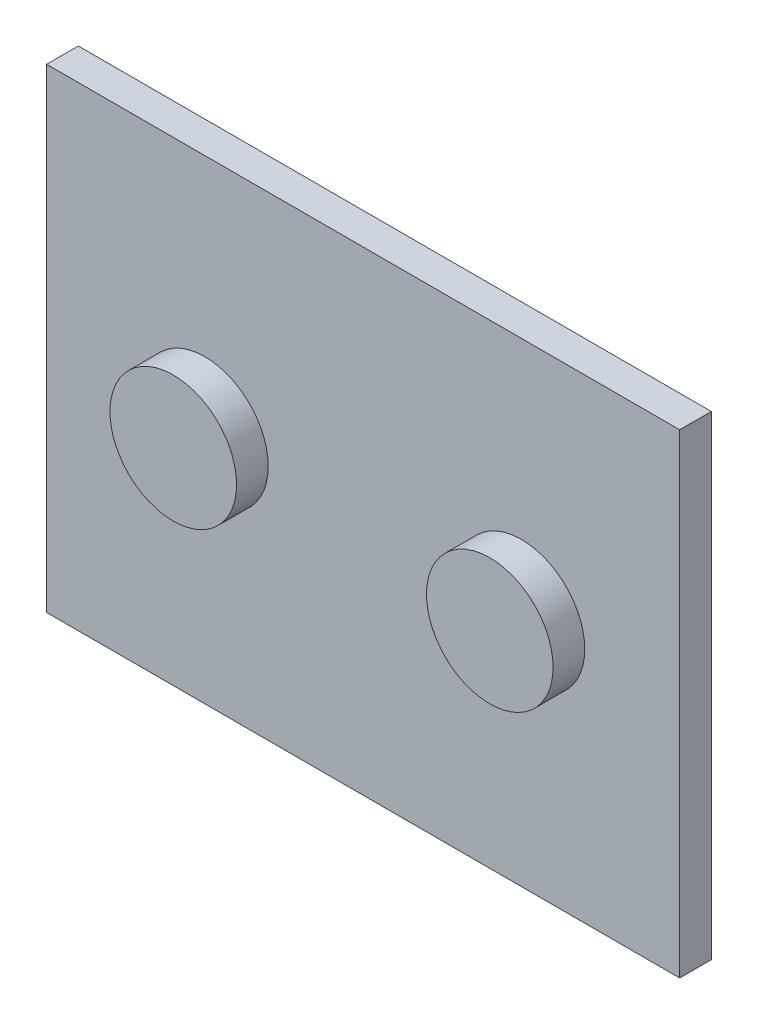
SolidWorks part; units mm, degrees
ref_plane "Front Plane" through (0, 0, 0) normal (0, 0, 1) x (1, 0, 0)
ref_plane "Top Plane" through (0, 0, 0) normal (0, 1, 0) x (1, 0, 0)
ref_plane "Right Plane" through (0, 0, 0) normal (1, 0, 0) x (0, 0, -1)
sketch "Sketch1" plane through (0, 0, 0) normal (0, 0, 1) x (1, 0, 0)
  line L1 (-101.369, 69.9691) -> (98.631, 69.9691)
  line L2 (-101.369, 69.9691) -> (-101.369, -80.0309)
  line L3 (-101.369, -80.0309) -> (98.631, -80.0309)
  line L4 (98.631, 69.9691) -> (98.631, -80.0309)
  dimension "D1" = 200
  dimension "D2" = 150
extrude "Boss-Extrude2" add sketch "Sketch1" along normal blind 10
sketch "Sketch2" plane through (0, 0, 10) normal (0, 0, 1) x (1, 0, 0)
  line L0 (-101.369, 69.9691) -> (98.631, -80.0309)
  line L1 (98.631, -80.0309) -> (98.631, 69.9691)
  line L2 (98.631, 69.9691) -> (-101.369, -80.0309)
  line L3 (-51.369, -5.0309) -> (48.631, -5.0309)
  circle A0 centre (-1.369, -5.0309) radius 50
  circle A1 centre (-51.369, -5.0309) radius 20
  circle A2 centre (48.631, -5.0309) radius 20
  dimension "D1" = 100
extrude "Boss-Extrude3" add sketch "Sketch2" along normal blind 10 contours A0 A2 | A0 A2 L3 | L3 A2 A0 | A1
sketch "Sketch3" plane through (0, 0, 20) normal (0, 0, 1) x (1, 0, 0)
  line L0 (-71.369, -5.0309) -> (-31.369, -5.0309)
  circle A0 centre (-51.369, -5.0309) radius 20 construction
  circle A1 centre (-51.369, -5.0309) radius 20 construction
  dimension "D1" = 40
